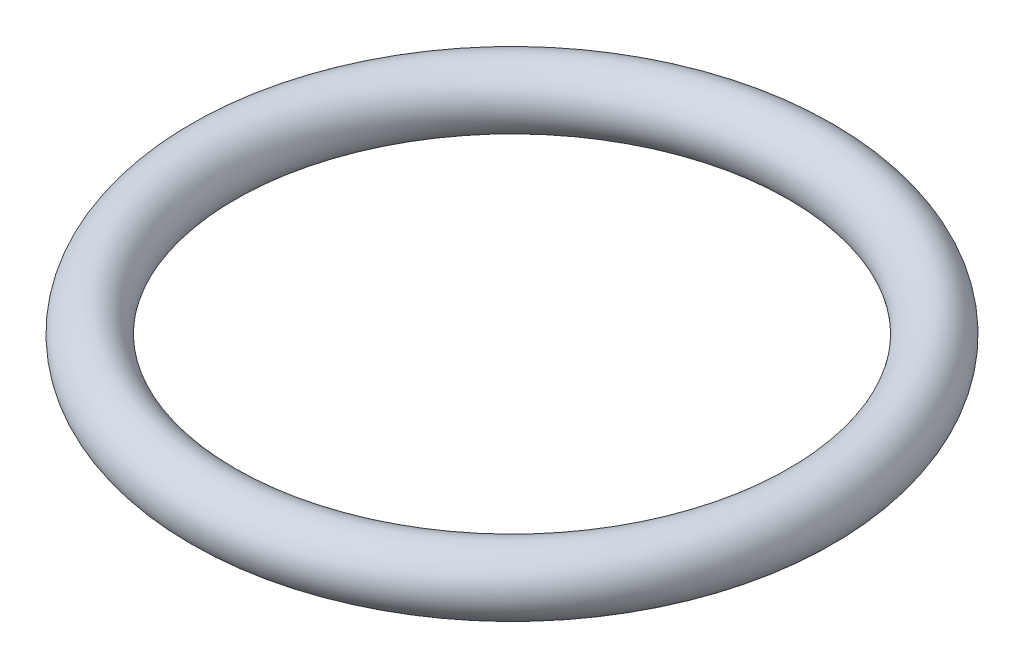
SolidWorks part; units mm, degrees
ref_plane "Front Plane" through (0, 0, 0) normal (0, 0, 1) x (1, 0, 0)
ref_plane "Top Plane" through (0, 0, 0) normal (0, 1, 0) x (1, 0, 0)
ref_plane "Right Plane" through (0, 0, 0) normal (1, 0, 0) x (0, 0, -1)
sketch "Sketch1" plane through (0, 0, 0) normal (0, 0, 1) x (1, 0, 0)
  line L0 (0, 0) -> (-8.585, 0) construction
  line L1 (0, 0) -> (0, 21.5583) construction
  circle A0 centre (-8.585, 0) radius 0.889
  dimension "D1" = 1.778
  dimension "D2" = 8.585
revolve "Revolve1" add sketch "Sketch1" angle 360 about L1
